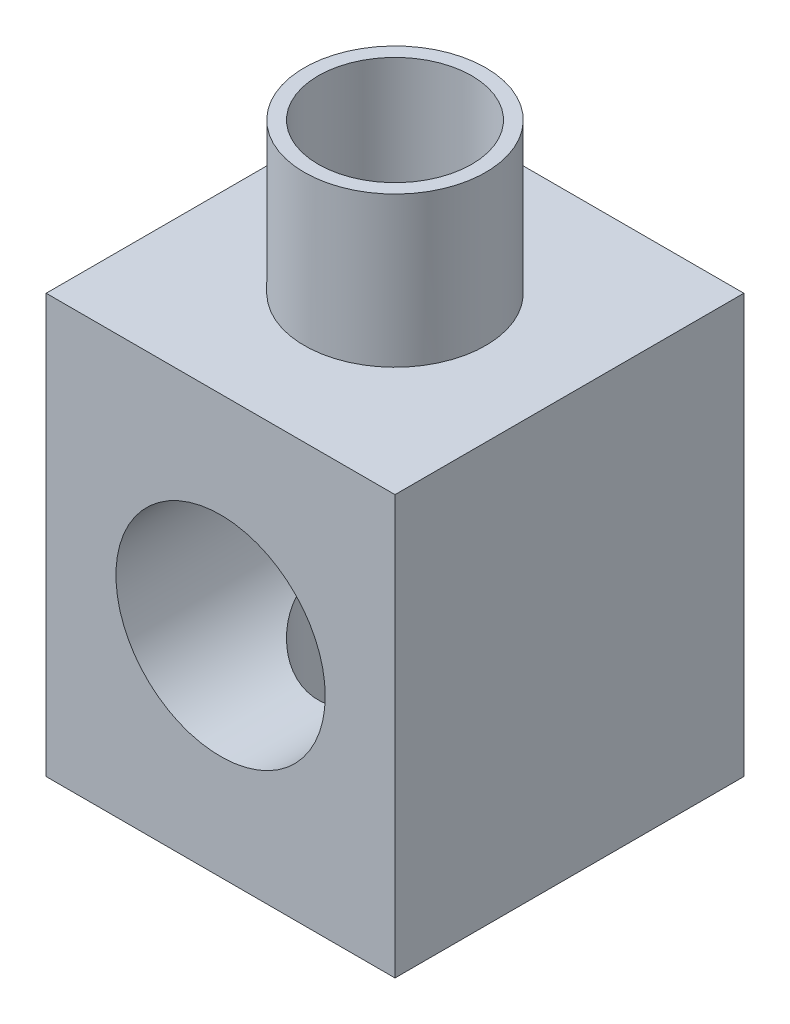
SolidWorks part; units mm, degrees
ref_plane "Alzado" through (0, 0, 0) normal (0, 0, 1) x (1, 0, 0)
ref_plane "Planta" through (0, 0, 0) normal (0, 1, 0) x (1, 0, 0)
ref_plane "Vista lateral" through (0, 0, 0) normal (1, 0, 0) x (0, 0, -1)
sketch "Croquis1" plane through (0, 0, 0) normal (0, 1, 0) x (1, 0, 0)
  line L1 (-25, -25) -> (25, -25)
  line L2 (-25, -25) -> (-25, 25)
  line L3 (-25, 25) -> (25, 25)
  line L4 (25, -25) -> (25, 25)
  line L5 (-25, -25) -> (25, 25) construction
  line L6 (-25, 25) -> (25, -25) construction
  circle A0 centre (0, 0) radius 11
  dimension "D1" = 22
  dimension "D2" = 50
  dimension "D3" = 50
extrude "Saliente-Extruir1" add sketch "Croquis1" along normal blind 60
sketch "Croquis3" plane through (0, 0, 25) normal (0, 0, 1) x (1, 0, 0)
  line L0 (0, 60) -> (0, 0) construction
  line L1 (-25, 60) -> (25, 60) construction
  circle A0 centre (0, 30) radius 15
  dimension "D1" = 30
extrude "Cortar-Extruir1" cut sketch "Croquis3" against normal blind 47
sketch "Croquis4" plane through (0, 0, -22) normal (0, 0, 1) x (1, 0, 0)
  circle A0 centre (0, 30) radius 4
  dimension "D1" = 8
extrude "Cortar-Extruir2" cut sketch "Croquis4" against normal blind 10
sketch "Croquis5" plane through (0, 60, 0) normal (0, 1, 0) x (1, 0, 0)
  circle A0 centre (0, 0) radius 11
  circle A1 centre (0, 0) radius 13
  dimension "D1" = 22
  dimension "D2" = 2
extrude "Saliente-Extruir3" add sketch "Croquis5" along normal blind 21.5
sketch "Croquis7" plane through (0, 0, 0) normal (0, -1, 0) x (1, 0, 0)
  circle A0 centre (0, 0) radius 11
  circle A1 centre (0, 0) radius 13
  dimension "D1" = 22
  dimension "D2" = 2
extrude "Saliente-Extruir4" add sketch "Croquis7" along normal blind 10
